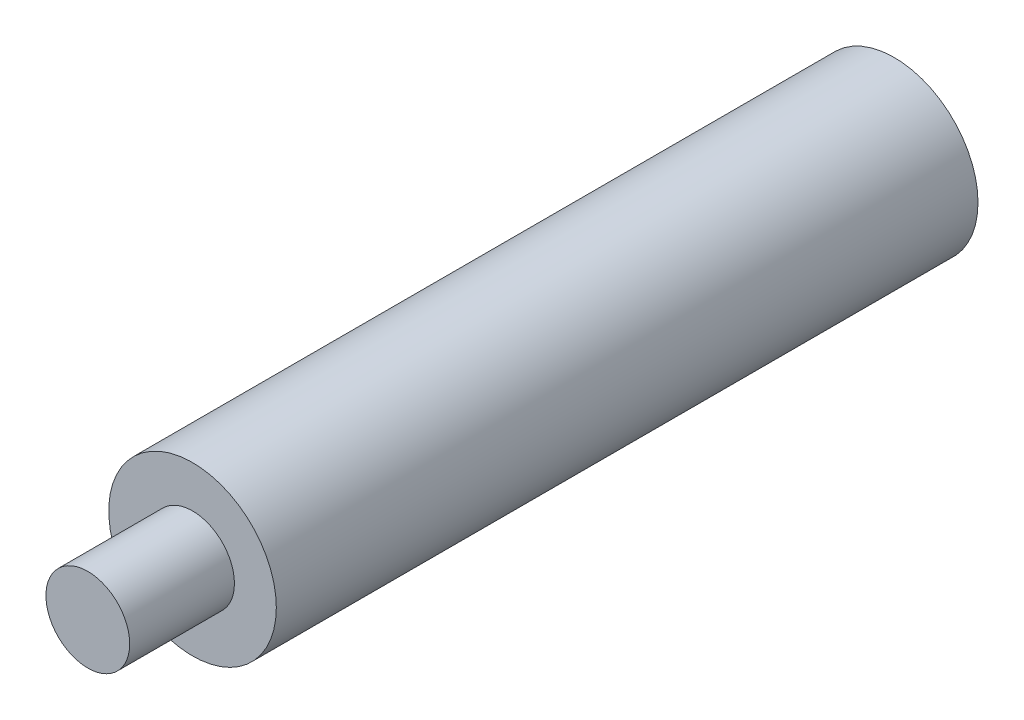
SolidWorks part; units mm, degrees
ref_plane "Front Plane" through (0, 0, 0) normal (0, 0, 1) x (1, 0, 0)
ref_plane "Top Plane" through (0, 0, 0) normal (0, 1, 0) x (1, 0, 0)
ref_plane "Right Plane" through (0, 0, 0) normal (1, 0, 0) x (0, 0, -1)
sketch "Sketch1" plane through (0, 0, 0) normal (0, 0, 1) x (1, 0, 0)
  circle A0 centre (0, 0) radius 4
  dimension "D1" = 8
extrude "Boss-Extrude1" add sketch "Sketch1" along normal blind 33.5
sketch "Sketch2" plane through (0, 0, 33.5) normal (0, 0, 1) x (1, 0, 0)
  circle A0 centre (0, 0) radius 2
  dimension "D1" = 4
extrude "Boss-Extrude2" add sketch "Sketch2" along normal blind 5
sketch "Sketch3" plane through (0, 0, 0) normal (0, 0, -1) x (-1, 0, 0)
  circle A0 centre (0, 0) radius 1.5
  dimension "D1" = 3
extrude "Cut-Extrude1" cut sketch "Sketch3" against normal blind 10
cosmetic thread "Cosmetic Thread2" parameters "D1"=8, "D2"=4
